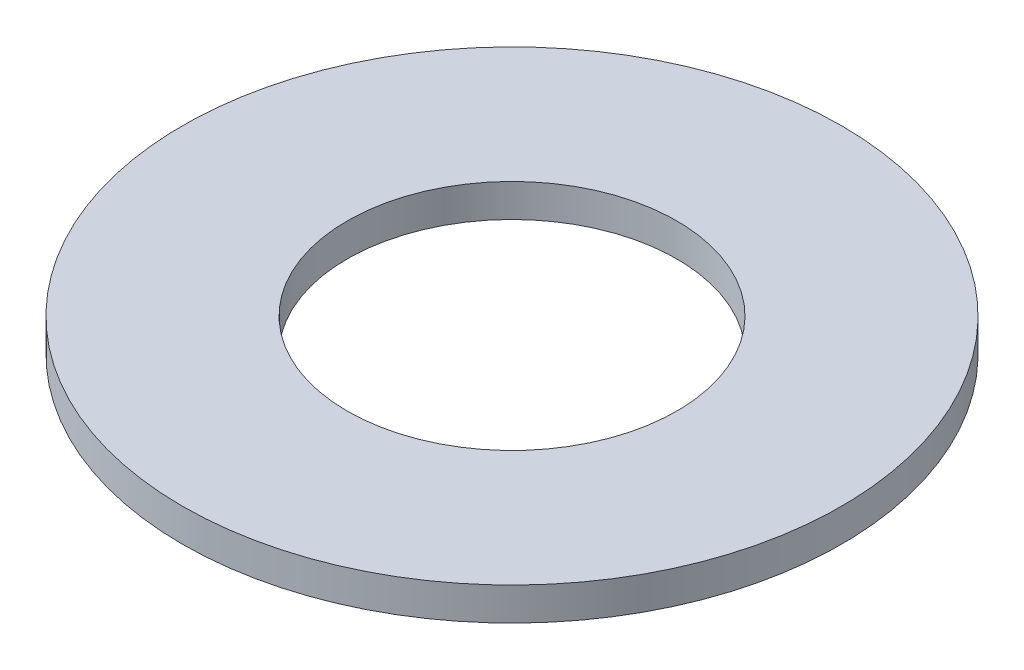
SolidWorks part; units mm, degrees
ref_plane "Front Plane" through (0, 0, 0) normal (0, 0, 1) x (1, 0, 0)
ref_plane "Top Plane" through (0, 0, 0) normal (0, 1, 0) x (1, 0, 0)
ref_plane "Right Plane" through (0, 0, 0) normal (1, 0, 0) x (0, 0, -1)
sketch "Sketch1" plane through (0, 0, 0) normal (0, 1, 0) x (1, 0, 0)
  circle A0 centre (0, 0) radius 5
  circle A1 centre (0, 0) radius 10
  dimension "D1" = 20
  dimension "D2" = 10
extrude "Boss-Extrude1" add sketch "Sketch1" along normal blind 1
